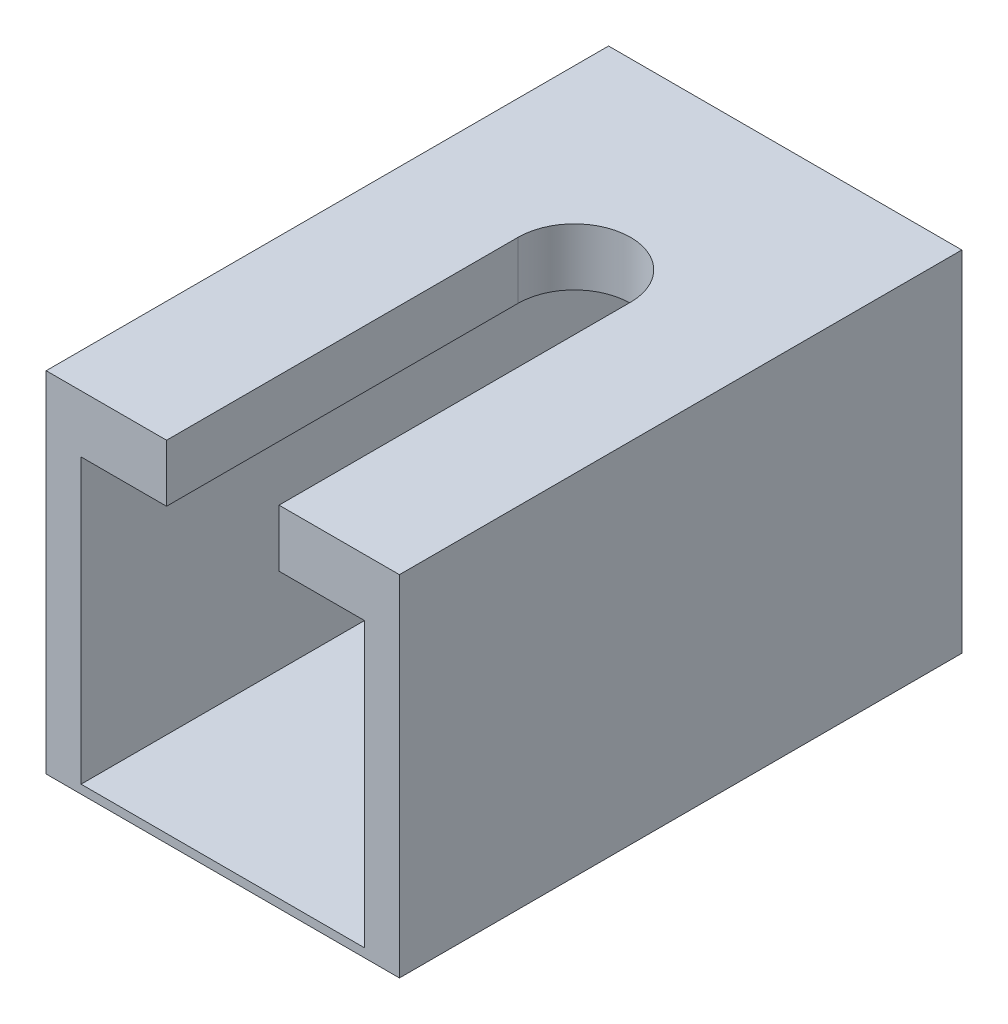
SolidWorks part; units mm, degrees
ref_plane "Front Plane" through (0, 0, 0) normal (0, 0, 1) x (1, 0, 0)
ref_plane "Top Plane" through (0, 0, 0) normal (0, 1, 0) x (1, 0, 0)
ref_plane "Right Plane" through (0, 0, 0) normal (1, 0, 0) x (0, 0, -1)
sketch "Sketch1" plane through (0, 0, 0) normal (0, 0, 1) x (1, 0, 0)
  line L1 (-6.35, 6.35) -> (6.35, 6.35) construction
  line L2 (-6.35, 6.35) -> (-6.35, -6.35) construction
  line L3 (-6.35, -6.35) -> (6.35, -6.35) construction
  line L4 (6.35, 6.35) -> (6.35, -6.35) construction
  line L5 (-6.35, 6.35) -> (6.35, -6.35) construction
  line L6 (-6.35, -6.35) -> (6.35, 6.35) construction
  line L7 (-6.4, 6.4) -> (6.4, 6.4)
  line L8 (-6.4, 6.4) -> (-6.4, -6.4)
  line L9 (-6.4, -6.4) -> (6.4, -6.4)
  line L10 (6.4, 6.4) -> (6.4, -6.4)
  line L11 (-6.4, 6.4) -> (6.4, -6.4) construction
  line L12 (-6.4, -6.4) -> (6.4, 6.4) construction
  line L13 (-7.9775, 8.9835) -> (7.9775, 8.9835)
  line L14 (-7.9775, 8.9835) -> (-7.9775, -6.7921)
  line L15 (-7.9775, -6.7921) -> (7.9775, -6.7921)
  line L16 (7.9775, 8.9835) -> (7.9775, -6.7921)
  point P0 (0, 0)
  point P6 (0, 0)
  point P11 (0, 0)
  dimension "D1" = 12.7
  dimension "D2" = 12.7
  dimension "D3" = 12.8
  dimension "D4" = 2.5835
  dimension "D5" = 1.5775
  dimension "D6" = 1.5775
  dimension "D7" = 0.3921
extrude "Boss-Extrude1" add sketch "Sketch1" along normal mid plane 25.4
sketch "Sketch2" plane through (0, 8.9835, 0) normal (0, 1, 0) x (1, 0, 0)
  line L1 (2.54, 3.175) -> (2.54, -12.7)
  line L2 (7.9775, -12.7) -> (-7.9775, -12.7) construction
  line L3 (2.54, -12.7) -> (-2.54, -12.7)
  line L4 (-2.54, -12.7) -> (-2.54, 3.175)
  line L5 (7.9775, 12.7) -> (-7.9775, 12.7) construction
  arc A1 (2.54, 3.175) -> (-2.54, 3.175) centre (0, 3.175) ccw
  dimension "D1" = 9.525
  dimension "D2" = 2.54
extrude "Cut-Extrude1" cut sketch "Sketch2" against normal blind 12.7
equation "\"D6@Sketch1\"=\"D5@Sketch1\""
